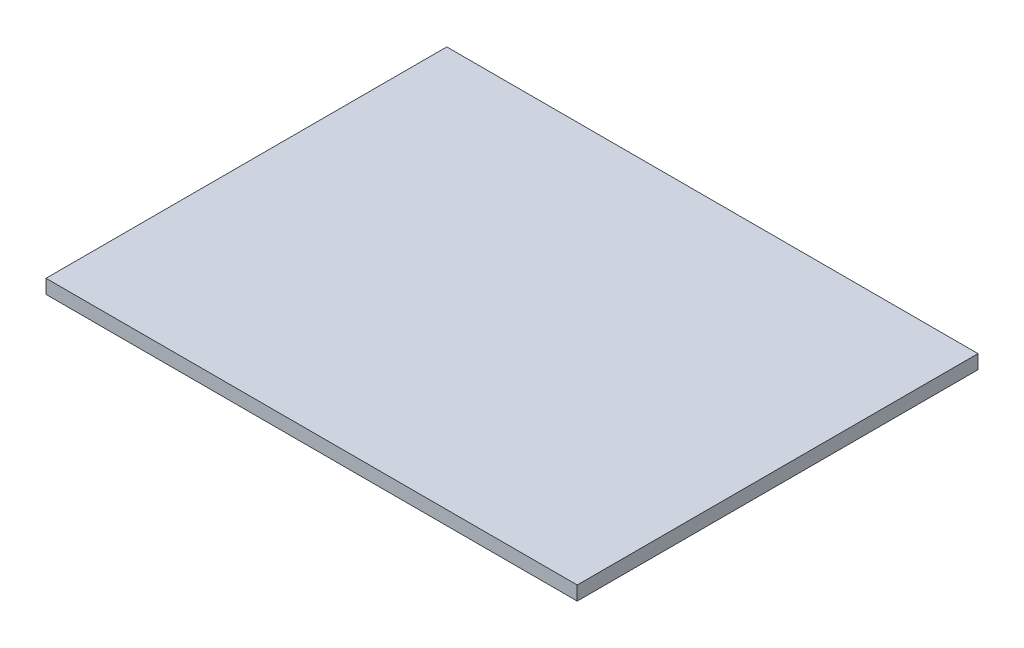
SolidWorks part; units mm, degrees
ref_plane "Front Plane" through (0, 0, 0) normal (0, 0, 1) x (1, 0, 0)
ref_plane "Top Plane" through (0, 0, 0) normal (0, 1, 0) x (1, 0, 0)
ref_plane "Right Plane" through (0, 0, 0) normal (1, 0, 0) x (0, 0, -1)
sketch "Sketch1" plane through (0, 0, 0) normal (0, 1, 0) x (1, 0, 0)
  line L1 (0, 0) -> (180.975, 0)
  line L2 (0, 0) -> (0, -136.525)
  line L3 (0, -136.525) -> (180.975, -136.525)
  line L4 (180.975, 0) -> (180.975, -136.525)
  dimension "D1" = 136.525
  dimension "D2" = 180.975
extrude "Boss-Extrude1" add sketch "Sketch1" along normal blind 4.7625 contours L1 L4 L3 L2
